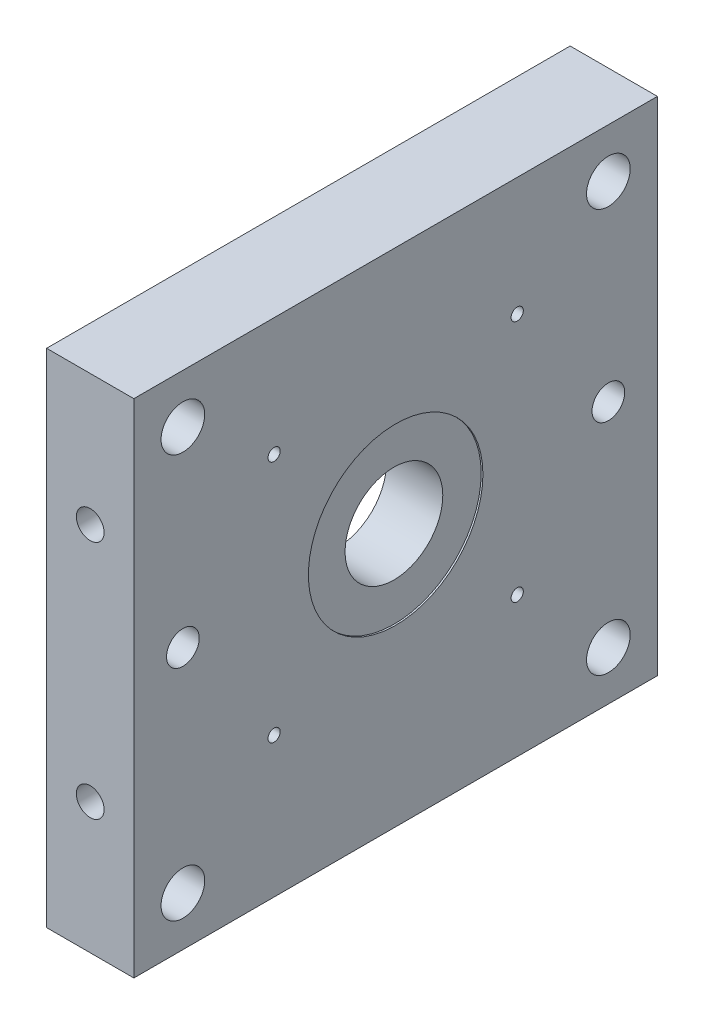
SolidWorks part; units mm, degrees
material "7079 Alloy"
ref_plane "Front Plane" through (0, 0, 0) normal (0, 0, 1) x (1, 0, 0)
ref_plane "Top Plane" through (0, 0, 0) normal (0, 1, 0) x (1, 0, 0)
ref_plane "Right Plane" through (0, 0, 0) normal (1, 0, 0) x (0, 0, -1)
sketch "Sketch1" plane through (0, 0, 0) normal (1, 0, 0) x (0, 0, -1)
  line L1 (0, 0) -> (76.2, 0)
  line L2 (0, 0) -> (0, -73.025)
  line L3 (0, -73.025) -> (76.2, -73.025)
  line L4 (76.2, 0) -> (76.2, -73.025)
  dimension "D1" = 76.2
  dimension "D2" = 73.025
extrude "Extrude1" add sketch "Sketch1" along normal blind 12.7
sketch "Sketch8" plane through (0, 0, 0) normal (-1, 0, 0) x (0, 0, 1)
  line L3 (-76.2, -73.025) -> (-76.2, 0) construction
  line L4 (-76.2, 0) -> (0, 0) construction
  circle A0 centre (-55.7961, -17.2339) radius 0.889
  circle A1 centre (-7.1374, -7.1374) radius 3.175
  circle A2 centre (-69.0626, -7.1374) radius 3.175
  circle A3 centre (-69.0626, -65.8876) radius 3.175
  circle A4 centre (-7.1374, -65.8876) radius 3.175
  circle A5 centre (-38.105, -34.925) radius 7.112
  circle A6 centre (-69.0626, -34.925) radius 2.3813
  circle A7 centre (-7.1374, -34.925) radius 2.3813
  circle A8 centre (-20.4139, -17.2339) radius 0.889
  circle A9 centre (-55.7961, -52.6161) radius 0.889
  circle A10 centre (-20.4139, -52.6161) radius 0.889
  dimension "D1" = 6.35
  dimension "D2" = 6.35
  dimension "D3" = 6.35
  dimension "D4" = 7.1374
  dimension "D5" = 6.35
  dimension "D6" = 4.7625
  dimension "D7" = 4.7625
  dimension "D8" = 14.224
  dimension "D22" = 25.019
  dimension "D28" = 25.019
  dimension "D9" = 7.1374
  dimension "D10" = 7.1374
  dimension "D11" = 69.0626
  dimension "D12" = 7.1374
  dimension "D13" = 7.1374
  dimension "D14" = 34.925
  dimension "D15" = 65.8876
  dimension "D16" = 38.095
  dimension "D17" = 34.925
  dimension "D18" = 69.0626
  dimension "D19" = 69.0626
  dimension "D20" = 34.925
  dimension "D21" = 65.8876
  dimension "D23" = 45
  dimension "D24" = 25.019
  dimension "D25" = 45
  dimension "D26" = 25.019
  dimension "D27" = 45
  dimension "D29" = 45
extrude "Cut-Extrude5" cut sketch "Sketch8" against normal blind 12.7
sketch "Sketch11" plane through (0, 0, 0) normal (-1, 0, 0) x (0, 0, 1)
  line L0 (-76.2, 0) -> (0, 0) construction
  line L1 (-76.2, -73.025) -> (-76.2, 0) construction
  circle A0 centre (-7.1374, -7.1374) radius 5.207
  circle A1 centre (-69.0626, -7.1374) radius 5.207
  circle A2 centre (-69.0626, -65.8876) radius 5.207
  circle A3 centre (-7.1374, -65.8876) radius 5.207
  dimension "D1" = 10.414
  dimension "D2" = 10.414
  dimension "D3" = 10.414
  dimension "D4" = 10.414
  dimension "D5" = 7.1374
  dimension "D6" = 7.1374
extrude "Cut-Extrude6" cut sketch "Sketch11" against normal blind 6.35
sketch "Sketch13" plane through (0, 0, 0) normal (-1, 0, 0) x (0, 0, 1)
  circle A0 centre (-38.105, -34.925) radius 17.4625
  dimension "D1" = 34.925
extrude "Cut-Extrude7" cut sketch "Sketch13" against normal blind 4.2545
sketch "Sketch14" plane through (12.7, 0, 0) normal (1, 0, 0) x (0, 0, -1)
  circle A0 centre (38.105, -34.925) radius 12.7
  dimension "D1" = 25.4
extrude "Cut-Extrude8" cut sketch "Sketch14" against normal blind 0.254
sketch "Sketch15" plane through (0, 0, 0) normal (0, 0, -1) x (-1, 0, 0)
  line L0 (9.7667, -36.5125) -> (-12.7, -36.5125) construction
  line L2 (0, 0) -> (0, -73.025) construction
  line L3 (-6.35, 0) -> (-6.35, -75.7476) construction
  line L4 (-12.7, 0) -> (0, 0) construction
  line L5 (-12.7, -73.025) -> (0, -73.025) construction
  line L6 (-12.7, 0) -> (-12.7, -73.025) construction
  circle A0 centre (-6.35, -19.05) radius 2.0193
  circle A1 centre (-6.35, -53.975) radius 2.0193
  dimension "D1" = 4.0386
  dimension "D2" = 36.5125
  dimension "D3" = 36.5125
  dimension "D4" = 6.35
extrude "Cut-Extrude9" cut sketch "Sketch15" along normal through all
